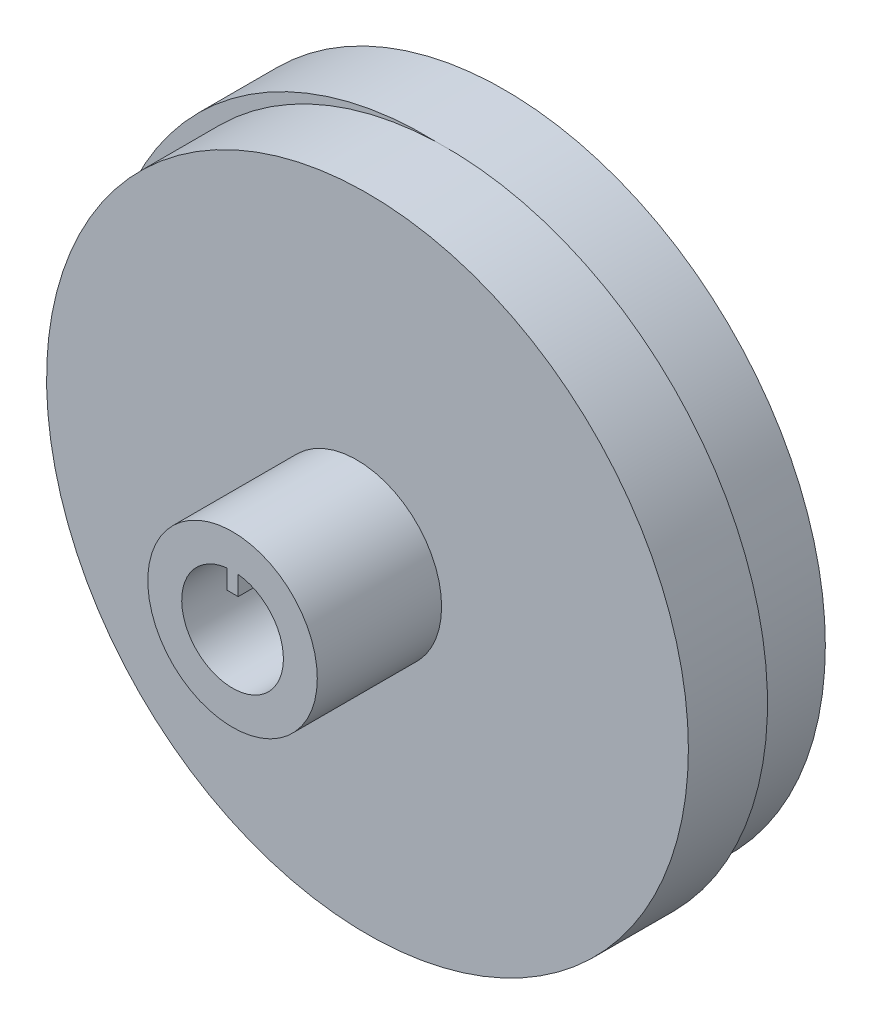
SolidWorks part; units mm, degrees
ref_plane "Front Plane" through (0, 0, 0) normal (0, 0, 1) x (1, 0, 0)
ref_plane "Top Plane" through (0, 0, 0) normal (0, 1, 0) x (1, 0, 0)
ref_plane "Right Plane" through (0, 0, 0) normal (1, 0, 0) x (0, 0, -1)
sketch "Sketch1" plane through (0, 0, 0) normal (0, 0, 1) x (1, 0, 0)
  circle A1 centre (0, 0) radius 28.4
  dimension "D1" = 56.8
extrude "Boss-Extrude1" add sketch "Sketch1" along normal blind 7
sketch "Sketch2" plane through (0, 0, 7) normal (0, 0, 1) x (1, 0, 0)
  line L0 (0, 18.846) -> (0, -14.7589) construction
  circle A0 centre (1.88, 0) radius 28.4
  dimension "D1" = 56.8
  dimension "D2" = 1.88
extrude "Boss-Extrude3" add sketch "Sketch2" along normal blind 7
sketch "Sketch4" plane through (0, 0, 14) normal (0, 0, 1) x (1, 0, 0)
  line L0 (16.7888, 0) -> (-13.7281, 0) construction
  line L1 (0.94, 18.6189) -> (0.94, -19.073) construction
  circle A0 centre (0.94, 0) radius 7.5
  dimension "D2" = 15
  dimension "D1" = 0.94
extrude "Boss-Extrude4" add sketch "Sketch4" along normal blind 11
sketch "Sketch5" plane through (0, 0, 14) normal (0, 0, 1) x (1, 0, 0)
  line L0 (-28.4, 0) -> (30.28, 0) construction
  line L1 (0.94, -22.4914) -> (0.94, 23.6342) construction
  arc A0 (0.94, 28.3844) -> (0.94, -28.3844) centre (0, 0) ccw construction
  circle A1 centre (1.88, 0) radius 28.4 construction
  dimension "D1" = 29.34
sketch "Sketch6" plane through (0, 0, 25) normal (0, 0, 1) x (1, 0, 0)
  line L0 (-28.4, 0) -> (30.28, 0) construction
  line L1 (0.44, 2.7701) -> (1.44, 2.7701)
  line L2 (1.44, 2.7701) -> (1.44, 4.4721)
  line L4 (0.44, 4.4721) -> (0.44, 2.7701)
  line L5 (0.94, -22.4914) -> (0.94, 23.6342) construction
  arc A0 (0.44, 4.4721) -> (1.44, 4.4721) centre (0.94, 0) ccw
  dimension "D1" = 9
  dimension "D2" = 0.5
  dimension "D3" = 1
extrude "Cut-Extrude1" cut sketch "Sketch6" against normal blind 10 contours A0 L2 L1 L4
